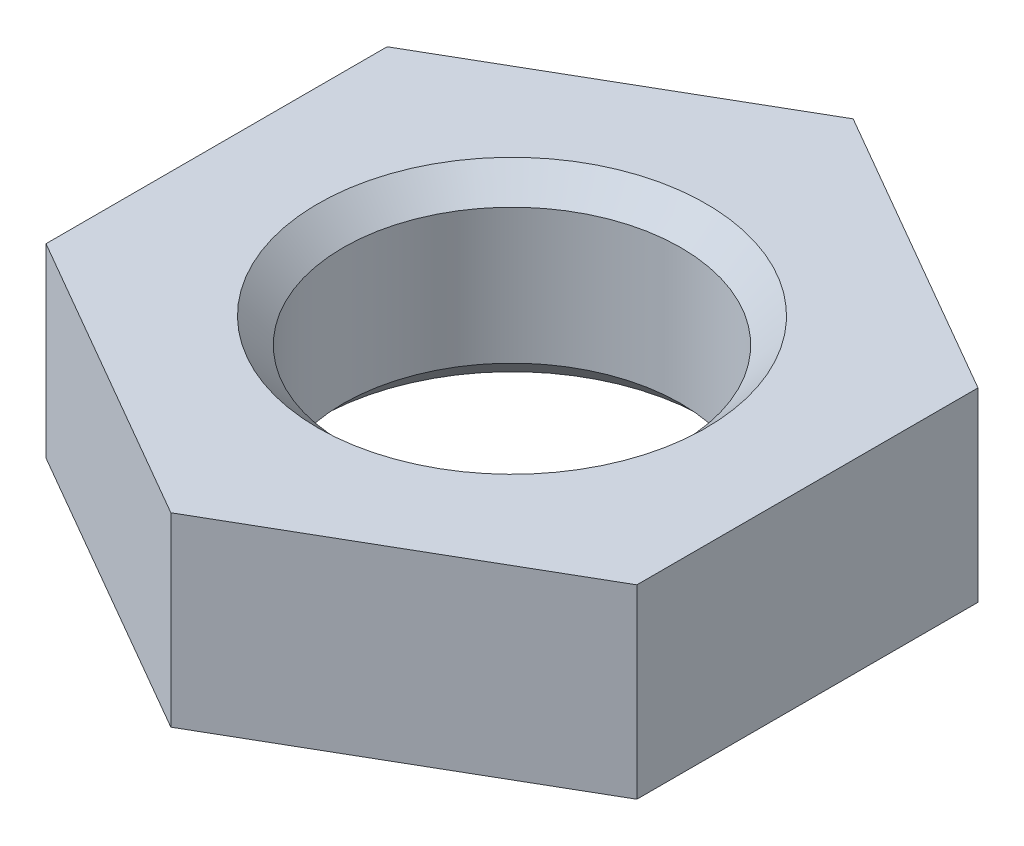
SolidWorks part; units mm, degrees
material "1023 Листовая углеродистая сталь (SS)"
ref_plane "Спереди" through (0, 0, 0) normal (0, 0, 1) x (1, 0, 0)
ref_plane "Сверху" through (0, 0, 0) normal (0, 1, 0) x (1, 0, 0)
ref_plane "Справа" through (0, 0, 0) normal (1, 0, 0) x (0, 0, -1)
sketch "Эскиз1" plane through (0, 0, 0) normal (0, 1, 0) x (1, 0, 0)
  line L0 (0, 0) -> (0, 19.4726) construction
  line L1 (-3.5, 2.0207) -> (-3.5, -2.0207)
  line L2 (-3.5, -2.0207) -> (0, -4.0415)
  line L3 (0, -4.0415) -> (3.5, -2.0207)
  line L4 (3.5, -2.0207) -> (3.5, 2.0207)
  line L5 (3.5, 2.0207) -> (0, 4.0415)
  line L6 (0, 4.0415) -> (-3.5, 2.0207)
  circle A0 centre (0, 0) radius 3.5 construction
  circle A1 centre (0, 0) radius 2
  dimension "D3" = 4
  dimension "D1" = 60
  dimension "D2" = 7
extrude "Бобышка-Вытянуть1" add sketch "Эскиз1" along normal blind 2.2
chamfer "Фаска1" distance 0.3 angle 45 2 edges at (0, 2.2, 2) (0, 0, 2)
